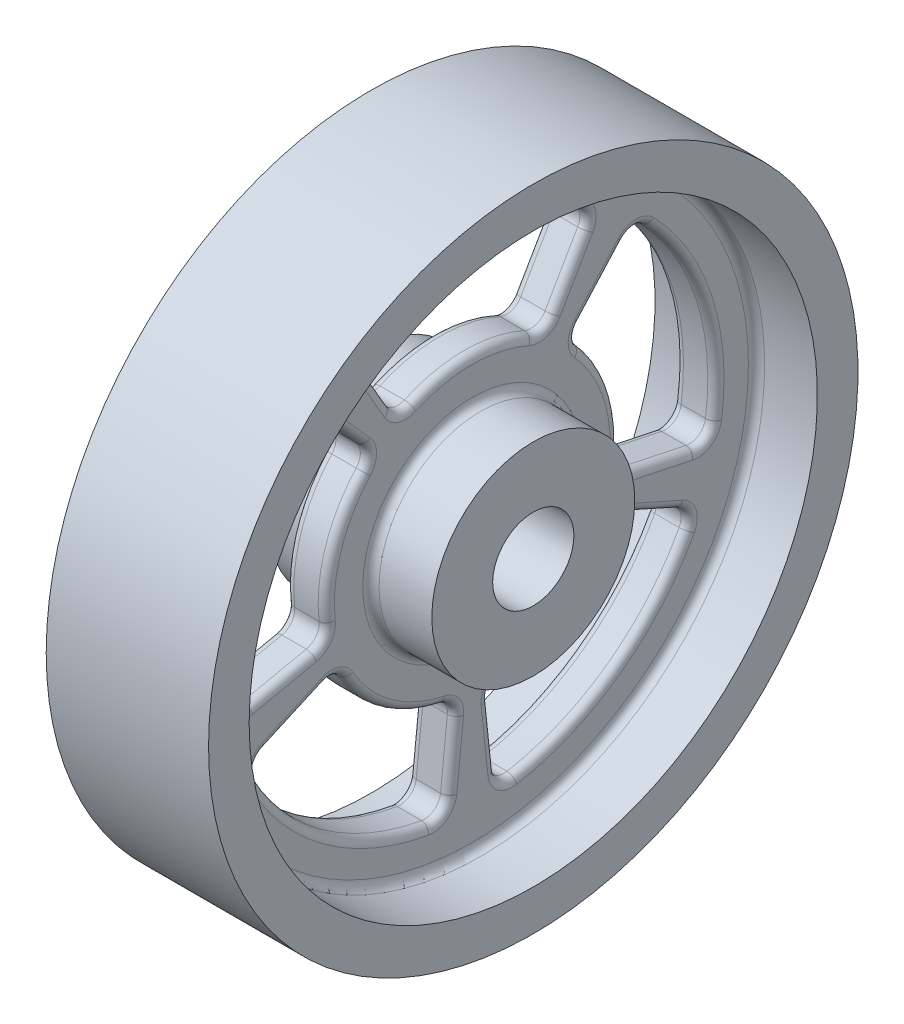
SolidWorks part; units mm, degrees
ref_plane "Front Plane" through (0, 0, 0) normal (0, 0, 1) x (1, 0, 0)
ref_plane "Top Plane" through (0, 0, 0) normal (0, 1, 0) x (1, 0, 0)
ref_plane "Right Plane" through (0, 0, 0) normal (1, 0, 0) x (0, 0, -1)
sketch "Sketch1" plane through (0, 0, 0) normal (0, 0, 1) x (1, 0, 0)
  line L0 (2.5, 35) -> (10, 35)
  line L1 (-10, 5) -> (10, 5)
  line L2 (-10, 5) -> (-10, 12.5)
  line L3 (-10, 12.5) -> (-2.5, 12.5)
  line L4 (10, 5) -> (10, 12.5)
  line L6 (-2.5, 12.5) -> (-2.5, 35)
  line L8 (2.5, 12.5) -> (2.5, 35)
  line L9 (-10, 35) -> (-2.5, 35)
  line L10 (-10, 35) -> (-10, 40)
  line L11 (-10, 40) -> (10, 40)
  line L12 (10, 35) -> (10, 40)
  line L13 (2.5, 12.5) -> (10, 12.5)
  line L14 (0, 0) -> (0, 14.9169) construction
  line L15 (0, 0) -> (16.1967, 0) construction
  dimension "D1" = 20
  dimension "D2" = 5
  dimension "D3" = 5
  dimension "D4" = 10
  dimension "D5" = 25
  dimension "D6" = 80
  dimension "D7" = 20
revolve "Revolve1" add sketch "Sketch1" angle 360 about L15
sketch "Sketch2" plane through (2.5, 0, 0) normal (1, 0, 0) x (0, 0, -1)
  line L0 (0, 0) -> (0, 43.2046) construction
  line L1 (-15, 25.9808) -> (-9, 15.5885)
  line L2 (9, 15.5885) -> (15, 25.9808)
  arc A1 (-15, 25.9808) -> (15, 25.9808) centre (0, 0) cw
  arc A2 (-9, 15.5885) -> (9, 15.5885) centre (0, 0) cw
  point P7 (0, 0)
  dimension "D1" = 30
  dimension "D2" = 18
  dimension "D3" = 60
  dimension "D4" = 30
extrude "Cut-Extrude1" cut sketch "Sketch2" against normal through all
fillet "Fillet2" radius 2 4 edges at (0, 25.9808, 15) (0, 15.5885, 9) (0, 25.9808, -15) (0, 15.5885, -9)
pattern_circular "CirPattern1" count 5 over 360 about axis through (0, 0, 0) along (1, 0, 0) of "Cut-Extrude1", "Fillet2"
fillet "Fillet3" radius 1 42 edges at (2.5, 0, 12.5) (2.5, 0, 35) (2.5, 16.3302, 8.8315) (2.5, 18, 0) (2.5, 16.3302, -8.8315) (2.5, 20.7102, -11.9571) (2.5, 25.7731, -14.1443) (2.5, 30, 0) (2.5, 25.7731, 14.1443) (2.5, 20.7102, 11.9571) (2.5, 13.4456, -12.8018) (2.5, 5.5623, -17.119) (2.5, -3.353, -18.26) (2.5, -4.972, -23.3915) (2.5, -5.4877, -28.8825) (2.5, 9.2705, -28.5317) (2.5, 21.4164, -20.1409) (2.5, 17.7717, -16.0017) (2.5, -8.0203, -16.7435) (2.5, -14.5623, -10.5801) (2.5, -18.4024, -2.4538) (2.5, -23.7831, -2.4997) (2.5, -29.1647, -3.7061) (2.5, -24.2705, -17.6336) (2.5, -12.5371, -26.592) (2.5, -9.7267, -21.8466) (2.5, -18.4024, 2.4538) (2.5, -14.5623, 10.5801) (2.5, -8.0203, 16.7435) (2.5, -9.7267, 21.8466) (2.5, -12.5371, 26.592) (2.5, -24.2705, 17.6336) (2.5, -29.1647, 3.7061) (2.5, -23.7831, 2.4997) (2.5, -3.353, 18.26) (2.5, 5.5623, 17.119) (2.5, 13.4456, 12.8018) (2.5, 17.7717, 16.0017) (2.5, 21.4164, 20.1409) (2.5, 9.2705, 28.5317) (2.5, -5.4877, 28.8825) (2.5, -4.972, 23.3915)
fillet "Fillet4" radius 1 42 edges at (-2.5, 0, 35) (-2.5, 0, 12.5) (-2.5, 16.3302, 8.8315) (-2.5, 20.7102, 11.9571) (-2.5, 25.7731, 14.1443) (-2.5, 30, 0) (-2.5, 25.7731, -14.1443) (-2.5, 20.7102, -11.9571) (-2.5, 16.3302, -8.8315) (-2.5, 18, 0) (-2.5, 13.4456, -12.8018) (-2.5, 17.7717, -16.0017) (-2.5, 21.4164, -20.1409) (-2.5, 9.2705, -28.5317) (-2.5, -5.4877, -28.8825) (-2.5, -4.972, -23.3915) (-2.5, -3.353, -18.26) (-2.5, 5.5623, -17.119) (-2.5, -8.0203, -16.7435) (-2.5, -9.7267, -21.8466) (-2.5, -12.5371, -26.592) (-2.5, -24.2705, -17.6336) (-2.5, -29.1647, -3.7061) (-2.5, -23.7831, -2.4997) (-2.5, -18.4024, -2.4538) (-2.5, -14.5623, -10.5801) (-2.5, -18.4024, 2.4538) (-2.5, -23.7831, 2.4997) (-2.5, -29.1647, 3.7061) (-2.5, -24.2705, 17.6336) (-2.5, -12.5371, 26.592) (-2.5, -9.7267, 21.8466) (-2.5, -8.0203, 16.7435) (-2.5, -14.5623, 10.5801) (-2.5, -3.353, 18.26) (-2.5, -4.972, 23.3915) (-2.5, -5.4877, 28.8825) (-2.5, 9.2705, 28.5317) (-2.5, 21.4164, 20.1409) (-2.5, 17.7717, 16.0017) (-2.5, 13.4456, 12.8018) (-2.5, 5.5623, 17.119)
